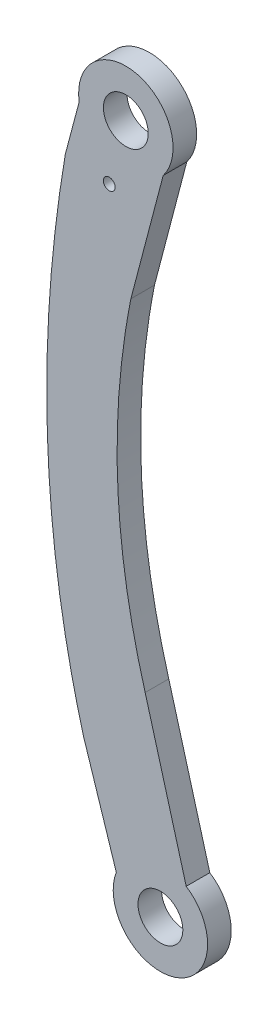
SolidWorks part; units mm, degrees
ref_plane "Front Plane" through (0, 0, 0) normal (0, 0, 1) x (1, 0, 0)
ref_plane "Top Plane" through (0, 0, 0) normal (0, 1, 0) x (1, 0, 0)
ref_plane "Right Plane" through (0, 0, 0) normal (1, 0, 0) x (0, 0, -1)
sketch "Sketch1" plane through (0, 0, 0) normal (0, 0, 1) x (1, 0, 0)
  line L0 (-5.8575, 13.9582) -> (-12.1265, -9.8963) construction
  line L5 (0, -100) -> (-5.9362, -82.0049) construction
  line L8 (1.2648, 12.0865) -> (-5.0042, -11.7681)
  line L9 (-12.7676, 16.5038) -> (-16.109, 3.9087)
  line L12 (-5.9677, -101.8214) -> (-13.027, -79.9923)
  line L14 (-2.5827, -68.3358) -> (5.3406, -96.7736)
  line L16 (-9.8175, 17.9182) -> (-1.8975, 17.9182)
  line L17 (-9.8175, 17.9182) -> (-9.8175, 9.9982)
  line L18 (-9.8175, 9.9982) -> (-1.8975, 9.9982)
  line L19 (-1.8975, 17.9182) -> (-1.8975, 9.9982)
  line L20 (-9.8175, 17.9182) -> (-1.8975, 9.9982) construction
  line L21 (-9.8175, 9.9982) -> (-1.8975, 17.9182) construction
  line L22 (-3.96, -96.04) -> (3.96, -96.04)
  line L23 (-3.96, -96.04) -> (-3.96, -103.96)
  line L24 (-3.96, -103.96) -> (3.96, -103.96)
  line L25 (3.96, -96.04) -> (3.96, -103.96)
  line L26 (-3.96, -96.04) -> (3.96, -103.96) construction
  line L27 (-3.96, -103.96) -> (3.96, -96.04) construction
  circle A4 centre (-5.8575, 13.9582) radius 3.8
  arc A8 (1.2648, 12.0865) -> (-12.7676, 16.5038) centre (-5.8575, 13.9582) ccw
  arc A15 (-5.9677, -101.8214) -> (6.2395, -100) centre (0, -100) ccw
  circle A17 centre (0, -100) radius 3.8
  circle A18 centre (0, -100) radius 6.2395
  circle A19 centre (-8.672, 3.2483) radius 1
  spline S1 degree 3 poles (-16.109, 3.9087) (-19.3777, -15.2425) (-20.6461, -43.8019) (-15.3573, -71.5641) (-13.027, -79.9923) knots 0 0 0 0 0.615831 0.891754 0.891754 0.891754 0.891754
  spline S2 degree 2 poles (-2.5827, -68.3358) (-10.6774, -40.3198) (-5.0042, -11.7681) knots 0 0 0 1 1 1
  dimension "D3" = 7.6
  dimension "D1" = 7.92
  dimension "D2" = 7.92
sketch "Sketch2" plane through (0, 0, 0) normal (0, 0, 1) x (1, 0, 0)
  line L1 (-3.96, -103.96) -> (3.96, -103.96)
  line L2 (-3.96, -103.96) -> (-3.96, -96.04)
  line L3 (-3.96, -96.04) -> (3.96, -96.04)
  line L4 (3.96, -103.96) -> (3.96, -96.04)
  line L5 (-3.96, -103.96) -> (3.96, -96.04) construction
  line L6 (-3.96, -96.04) -> (3.96, -103.96) construction
  line L7 (-9.8175, 9.9982) -> (-1.8975, 9.9982)
  line L8 (-9.8175, 9.9982) -> (-9.8175, 17.9182)
  line L9 (-9.8175, 17.9182) -> (-1.8975, 17.9182)
  line L10 (-1.8975, 9.9982) -> (-1.8975, 17.9182)
  line L11 (-9.8175, 9.9982) -> (-1.8975, 17.9182) construction
  line L12 (-9.8175, 17.9182) -> (-1.8975, 9.9982) construction
  circle A0 centre (0, -100) radius 8
  circle A1 centre (-5.8575, 13.9582) radius 8
extrude "Boss-Extrude1" add sketch "Sketch1" along normal mid plane 4 contours L14 S2 L8 A8 L9 S1 L12 A18 L16 L19 L18 L17 A19 | A15 A18 L22 L25 L24 L23 | L25 L22 L23 L24 A17 | L19 L16 L17 L18 A4
extrude "Boss-Extrude2" add sketch "Sketch2" along normal mid plane 4
